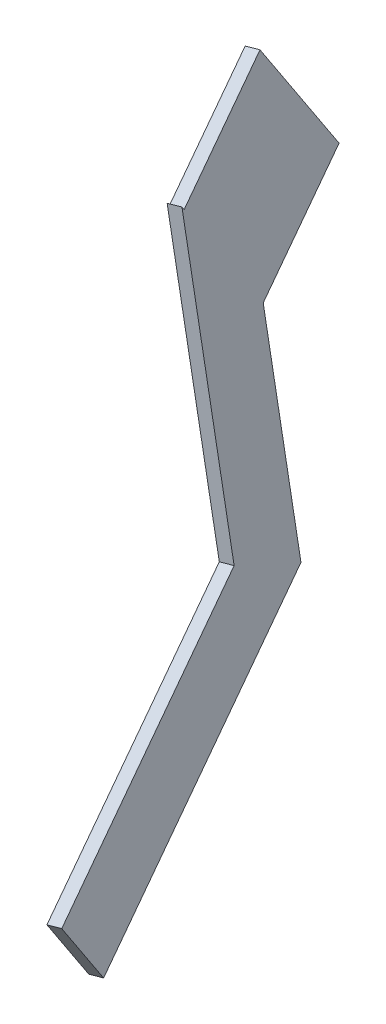
SolidWorks part; units mm, degrees
ref_plane "Front Plane" through (0, 0, 0) normal (0, 0, 1) x (1, 0, 0)
ref_plane "Top Plane" through (0, 0, 0) normal (0, 1, 0) x (1, 0, 0)
ref_plane "Right Plane" through (0, 0, 0) normal (1, 0, 0) x (0, 0, -1)
ref_plane "Plane1" through (-68.394, -9.004, 13.6994) normal (-0.9725, -0.128, 0.1948) x (0.1931, 0.0254, 0.9808)
sketch "Sketch1" plane through (-68.394, -9.004, 13.6994) normal (-0.9725, -0.128, 0.1948) x (0.1931, 0.0254, 0.9808)
  line L11 (318.4451, -558.8252) -> (321.2449, -554.6826) construction
  line L16 (94.926, -386.9954) -> (88.5747, -506.056)
  line L17 (94.926, -386.9954) -> (94.0536, -388.2862)
  line L18 (62.3089, -435.2548) -> (57.7131, -521.407)
  line L19 (57.7131, -521.407) -> (168.7828, -596.4756)
  line L20 (88.5747, -506.056) -> (185.5818, -571.6202)
  line L21 (168.7828, -596.4756) -> (185.5818, -571.6202)
  line L22 (62.3089, -435.2548) -> (19.6082, -406.3946)
  line L23 (138.9718, -431.4897) -> (99.7002, -404.9473) construction
  line L24 (270.8479, -629.2489) -> (90.7052, -507.496) construction
  line L25 (-352.4322, -83.4325) -> (386.0548, -582.5535) construction
  line L26 (94.926, -386.9954) -> (94.0536, -388.2862) construction
  line L28 (138.9718, -431.4897) -> (136.1719, -435.6323) construction
  line L29 (19.6082, -406.3946) -> (51.3528, -359.426)
  line L30 (94.0536, -388.2862) -> (51.3528, -359.426)
  line L31 (62.3089, -435.2548) -> (1.0291, -525.9229) construction
  point P2 (19.6082, -406.3946)
  dimension "D1" = 1
  dimension "D2" = 31
  dimension "D3" = 30
  dimension "D4" = 30
  dimension "D5" = 56.6902
  dimension "D6" = 51.539
extrude "Boss-Extrude1" add sketch "Sketch1" against normal blind 5
